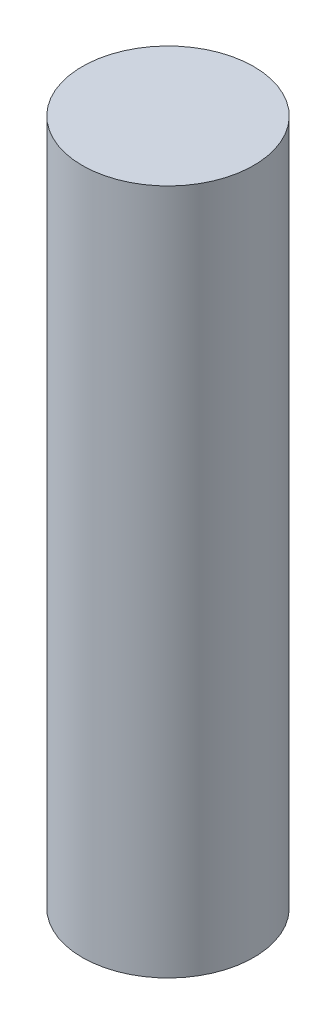
SolidWorks part; units mm, degrees
ref_plane "Face" through (0, 0, 0) normal (0, 0, 1) x (1, 0, 0)
ref_plane "Dessus" through (0, 0, 0) normal (0, 1, 0) x (1, 0, 0)
ref_plane "Droite" through (0, 0, 0) normal (1, 0, 0) x (0, 0, -1)
sketch "Esquisse2" plane through (0, 4.6576, 0) normal (0, -1, 0) x (1, 0, 0)
  circle A0 centre (-0.3894, -13.48) radius 1.25
  dimension "D1" = 2.5
extrude "Extrusion1" add sketch "Esquisse2" along normal blind 10
